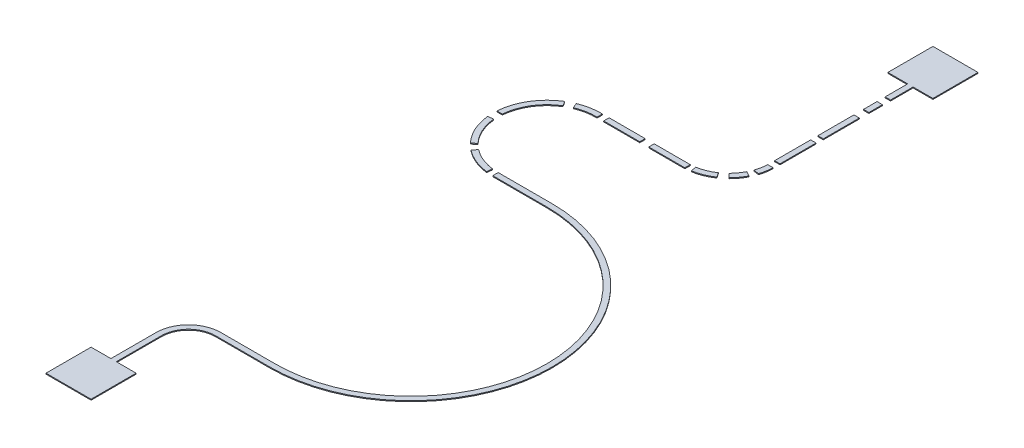
SolidWorks part; units mm, degrees
ref_plane "Front Plane" through (0, 0, 0) normal (0, 0, 1) x (1, 0, 0)
ref_plane "Top Plane" through (0, 0, 0) normal (0, 1, 0) x (1, 0, 0)
ref_plane "Right Plane" through (0, 0, 0) normal (1, 0, 0) x (0, 0, -1)
sketch "Sketch1" plane through (0, 0, 0) normal (0, 1, 0) x (1, 0, 0)
  line L1 (-103.8961, 163.961) -> (146.1039, 163.961)
  line L2 (-103.8961, 163.961) -> (-103.8961, -86.039)
  line L3 (-103.8961, -86.039) -> (146.1039, -86.039)
  line L4 (146.1039, 163.961) -> (146.1039, -86.039)
  dimension "D1" = 250
  dimension "D2" = 250
extrude "Boss-Extrude1" add sketch "Sketch1" along normal blind 5
sketch "Sketch2" plane through (0, 5, 0) normal (0, 1, 0) x (1, 0, 0)
  line L0 (146.1039, 163.961) -> (-103.8961, 163.961) construction
  line L1 (6.1039, 163.961) -> (36.1039, 163.961)
  line L2 (6.1039, 163.961) -> (6.1039, 413.961)
  line L3 (6.1039, 413.961) -> (36.1039, 413.961)
  line L4 (36.1039, 163.961) -> (36.1039, 413.961)
  line L5 (-103.8961, 163.961) -> (-103.8961, -86.039) construction
  dimension "D1" = 30
  dimension "D2" = 110
  dimension "D3" = 250
extrude "Boss-Extrude2" add sketch "Sketch2" against normal blind 5 separate body
sketch "Sketch6" plane through (0, 0, 0) normal (0, 1, 0) x (1, 0, 0)
  line L9 (186.3724, 594.2295) -> (186.3724, 564.2295)
  line L14 (6.1039, 413.961) -> (6.1039, 163.961)
  line L15 (6.1039, 163.961) -> (36.1039, 163.961)
  line L16 (36.1039, 163.961) -> (36.1039, 413.961)
  line L17 (36.1039, 413.961) -> (6.1039, 413.961)
  line L21 (36.1039, 413.961) -> (6.1039, 413.961)
  arc A0 (36.1039, 413.961) -> (186.3724, 564.2295) centre (186.3724, 413.961) cw
  arc A1 (6.1039, 413.961) -> (186.3724, 594.2295) centre (186.3724, 413.961) cw
  dimension "D1" = 30
  dimension "D2" = 0
extrude "Boss-Extrude3" add sketch "Sketch6" along normal blind 5
sketch "Sketch7" plane through (0, 0, 0) normal (0, 1, 0) x (1, 0, 0)
  line L1 (186.3724, 594.2295) -> (486.3724, 594.2295)
  line L2 (186.3724, 594.2295) -> (186.3724, 564.2295)
  line L3 (186.3724, 564.2295) -> (486.3724, 564.2295)
  line L4 (486.3724, 594.2295) -> (486.3724, 564.2295)
  dimension "D1" = 300
extrude "Boss-Extrude4" add sketch "Sketch7" along normal blind 5
sketch "Sketch8" plane through (0, 0, 0) normal (0, 1, 0) x (1, 0, 0)
  line L0 (486.3724, 2131.6071) -> (486.3724, 2101.6071)
  line L7 (6.1039, 413.961) -> (6.1039, 163.961)
  line L8 (6.1039, 163.961) -> (36.1039, 163.961)
  line L9 (36.1039, 163.961) -> (36.1039, 413.961)
  line L10 (186.3724, 564.2295) -> (486.3724, 564.2295)
  line L11 (486.3724, 564.2295) -> (486.3724, 594.2295)
  line L12 (486.3724, 594.2295) -> (186.3724, 594.2295)
  line L13 (6.1039, 413.961) -> (6.1039, 163.961)
  line L14 (6.1039, 163.961) -> (36.1039, 163.961)
  line L15 (36.1039, 163.961) -> (36.1039, 413.961)
  line L16 (186.3724, 564.2295) -> (486.3724, 564.2295)
  line L18 (486.3724, 594.2295) -> (186.3724, 594.2295)
  arc A0 (486.3724, 594.2295) -> (486.3724, 2101.6071) centre (486.3724, 1347.9183) ccw
  arc A1 (486.3724, 564.2295) -> (486.3724, 2131.6071) centre (486.3724, 1347.9183) ccw
  arc A4 (186.3724, 564.2295) -> (36.1039, 413.961) centre (186.3724, 413.961) ccw
  arc A5 (186.3724, 594.2295) -> (6.1039, 413.961) centre (186.3724, 413.961) ccw
  arc A6 (186.3724, 564.2295) -> (36.1039, 413.961) centre (186.3724, 413.961) ccw
  arc A7 (186.3724, 594.2295) -> (6.1039, 413.961) centre (186.3724, 413.961) ccw
  dimension "D2" = 753.6888
  dimension "D1" = 0
extrude "Boss-Extrude5" add sketch "Sketch8" along normal blind 5
sketch "Sketch10" plane through (0, 0, 0) normal (0, 1, 0) x (1, 0, 0)
  line L0 (486.3724, 2131.6071) -> (486.3724, 2101.6071) construction
  line L1 (186.3724, 2131.6083) -> (486.3724, 2131.6083)
  line L2 (186.3724, 2131.6083) -> (186.3724, 2101.6083)
  line L3 (186.3724, 2101.6083) -> (486.3724, 2101.6083)
  line L4 (486.3724, 2131.6083) -> (486.3724, 2101.6083)
  arc A0 (486.3724, 594.2295) -> (486.3724, 2101.6071) centre (486.3724, 1347.9183) ccw construction
  dimension "D1" = 753.69
  dimension "D2" = 0
  dimension "D3" = 30
  dimension "D4" = 300
extrude "Boss-Extrude6" add sketch "Sketch10" along normal blind 5
sketch "Sketch11" plane through (0, 0, 0) normal (0, 1, 0) x (1, 0, 0)
  line L0 (194.1382, 2702.1511) -> (194.1382, 2672.1399)
  line L1 (149.5323, 2103.8764) -> (153.2124, 2133.6498)
  line L3 (186.3724, 2131.6083) -> (186.3724, 2101.6083)
  line L4 (3.4402, 2163.7516) -> (21.7139, 2187.5439)
  line L5 (-31.7323, 2195.4755) -> (-9.9452, 2216.0988)
  line L6 (-112.5177, 2372.6417) -> (-82.6607, 2375.5674)
  line L7 (-113.1295, 2424.1046) -> (-83.0382, 2424.1046)
  line L8 (-31.9979, 2608.1034) -> (-10.1843, 2587.5081)
  line L9 (29.2713, 2657.8837) -> (44.9646, 2632.3157)
  line L10 (71.6057, 2679.4577) -> (83.0701, 2651.7347)
  arc A0 (186.3724, 2131.6083) -> (194.1382, 2672.1399) centre (186.3724, 2401.9299) cw
  arc A1 (186.3724, 2101.6083) -> (194.1382, 2702.1511) centre (186.3724, 2401.9299) cw
  point P9 (186.3724, 2116.6083)
  point P10 (151.3724, 2118.7631)
  point P13 (12.577, 2175.6477)
  point P16 (-20.8388, 2205.7871)
  point P19 (-97.5892, 2374.1046)
  point P22 (-98.0839, 2424.1046)
  point P25 (-21.0911, 2597.8058)
  point P28 (37.1179, 2645.0997)
  point P31 (77.3379, 2665.5962)
  dimension "D1" = 35
  dimension "D2" = 150
  dimension "D3" = 45
  dimension "D4" = 175
  dimension "D5" = 50
  dimension "D6" = 190
  dimension "D7" = 30
  dimension "D8" = 75
  dimension "D9" = 45
  dimension "D10" = 270.3216
extrude "Boss-Extrude7" add sketch "Sketch11" along normal blind 5 separate body contours A1 L1 A0 L4 | A1 L5 A0 L6 | A1 L7 A0 L8 | A1 L10 A0 L0 | A1 L8 A0 L9
sketch "Sketch12" plane through (0, 0, 0) normal (0, 1, 0) x (1, 0, 0)
  line L0 (194.1382, 2702.1511) -> (194.1382, 2672.1399) construction
  line L1 (231.1382, 2702.2499) -> (431.1382, 2702.2499)
  line L2 (231.1382, 2702.2499) -> (231.1382, 2672.2499)
  line L3 (231.1382, 2672.2499) -> (431.1382, 2672.2499)
  line L4 (431.1382, 2702.2499) -> (431.1382, 2672.2499)
  line L6 (481.1382, 2702.2499) -> (681.1382, 2702.2499)
  line L7 (481.1382, 2702.2499) -> (481.1382, 2672.2499)
  line L8 (481.1382, 2672.2499) -> (681.1382, 2672.2499)
  line L9 (681.1382, 2702.2499) -> (681.1382, 2672.2499)
  arc A0 (194.1382, 2672.1399) -> (83.0701, 2651.7347) centre (186.3724, 2401.9299) ccw construction
  dimension "D1" = 270.32
  dimension "D2" = 30
  dimension "D3" = 37
  dimension "D4" = 200
  dimension "D5" = 200
  dimension "D6" = 50
extrude "Boss-Extrude8" add sketch "Sketch12" along normal blind 5 separate body
sketch "Sketch13" plane through (0, 0, 0) normal (0, 1, 0) x (1, 0, 0)
  line L0 (896.0719, 2917.1836) -> (926.0719, 2917.1836)
  line L1 (713.6379, 2675.6262) -> (708.6385, 2705.1799)
  line L2 (681.1382, 2702.2499) -> (681.1382, 2672.2499)
  line L3 (814.5248, 2716.1869) -> (797.676, 2740.9766)
  line L4 (851.5246, 2746.7972) -> (830.3301, 2767.9917)
  line L5 (898.0935, 2810.6844) -> (871.9672, 2825.4293)
  line L6 (913.6156, 2847.8842) -> (883.6156, 2852.7413)
  arc A0 (681.1382, 2702.2499) -> (896.0719, 2917.1836) centre (671.0719, 2927.2499) ccw
  arc A1 (681.1382, 2672.2499) -> (926.0719, 2917.1836) centre (671.0719, 2927.2499) ccw
  point P9 (711.1382, 2690.4031)
  point P14 (840.9273, 2757.3945)
  point P17 (885.0303, 2818.0569)
  point P20 (898.6156, 2850.3127)
  dimension "D1" = 30
  dimension "D2" = 100
  dimension "D3" = 45
  dimension "D4" = 30
  dimension "D5" = 75
  dimension "D6" = 30
  dimension "D7" = 35
  dimension "D8" = 225
extrude "Boss-Extrude9" add sketch "Sketch13" along normal blind 5 separate body contours L1 A1 L3 A0 | L4 A1 L5 A0 | L6 A1 L0 A0
sketch "Sketch14" plane through (0, 0, 0) normal (0, 1, 0) x (1, 0, 0)
  line L1 (896.0719, 3155.1318) -> (926.0719, 3155.1318)
  line L2 (896.0719, 3155.1318) -> (896.0719, 2955.1318)
  line L3 (896.0719, 2955.1318) -> (926.0719, 2955.1318)
  line L4 (926.0719, 3155.1318) -> (926.0719, 2955.1318)
  line L5 (896.0719, 3395.1318) -> (926.0719, 3395.1318)
  line L6 (896.0719, 3395.1318) -> (896.0719, 3195.1318)
  line L7 (896.0719, 3195.1318) -> (926.0719, 3195.1318)
  line L8 (926.0719, 3395.1318) -> (926.0719, 3195.1318)
  line L9 (896.0719, 3523.2119) -> (926.0719, 3523.2119)
  line L10 (896.0719, 3523.2119) -> (896.0719, 3448.2119)
  line L11 (896.0719, 3448.2119) -> (926.0719, 3448.2119)
  line L12 (926.0719, 3523.2119) -> (926.0719, 3448.2119)
  line L13 (926.0719, 3568.2119) -> (896.0719, 3568.2119)
  line L14 (926.0719, 3568.2119) -> (926.0719, 3693.2119)
  line L15 (926.0719, 3693.2119) -> (896.0719, 3693.2119)
  line L16 (896.0719, 3568.2119) -> (896.0719, 3693.2119)
  line L17 (786.0719, 3943.2119) -> (1036.0719, 3943.2119)
  line L18 (786.0719, 3943.2119) -> (786.0719, 3693.2119)
  line L19 (786.0719, 3693.2119) -> (1036.0719, 3693.2119)
  line L20 (1036.0719, 3943.2119) -> (1036.0719, 3693.2119)
  arc A0 (883.6156, 2852.7413) -> (896.0719, 2917.1836) centre (671.0719, 2927.2499) ccw construction
  dimension "D1" = 225
  dimension "D2" = 30
  dimension "D3" = 200
  dimension "D4" = 30
  dimension "D5" = 40
  dimension "D6" = 200
  dimension "D7" = 30
  dimension "D8" = 0
  dimension "D9" = 75
  dimension "D10" = 45
  dimension "D11" = 125
  dimension "D12" = 250
  dimension "D13" = 110
  dimension "D14" = 30
  dimension "D15" = 250
extrude "Boss-Extrude10" add sketch "Sketch14" along normal blind 5 separate body contours L4 L1 L2 L3 | L8 L5 L6 L7 | L12 L9 L10 L11 | L20 L17 L18 L19 L15
